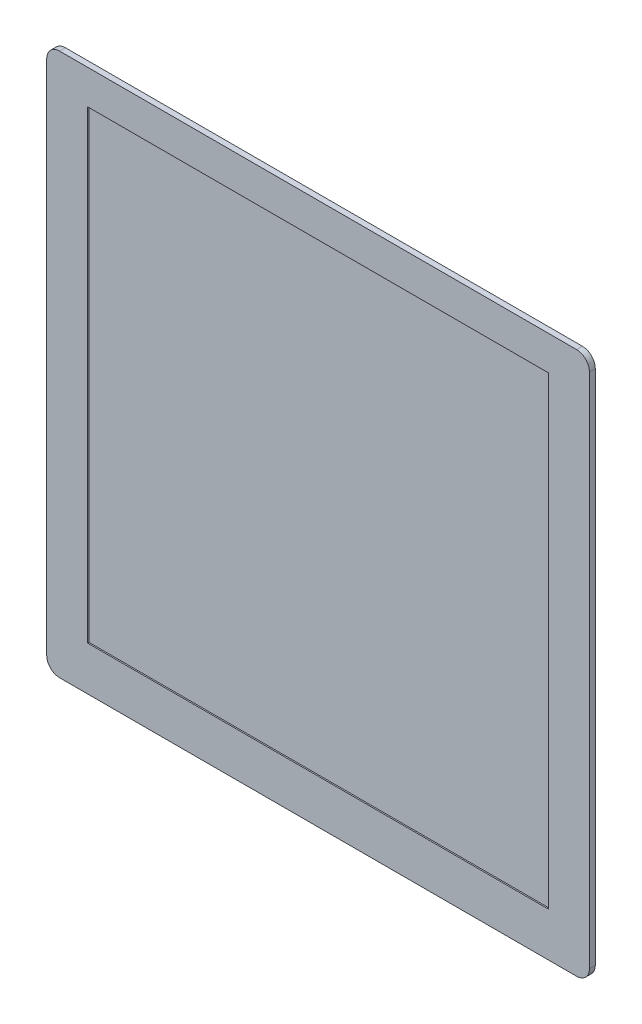
SolidWorks part; units mm, degrees
material "Plastique personnalisé"
ref_plane "Plan de face" through (0, 0, 0) normal (0, 0, 1) x (1, 0, 0)
ref_plane "Plan de dessus" through (0, 0, 0) normal (0, 1, 0) x (1, 0, 0)
ref_plane "Plan de droite" through (0, 0, 0) normal (1, 0, 0) x (0, 0, -1)
sketch "Esquisse1" plane through (0, 0, 0) normal (0, 0, 1) x (1, 0, 0)
  line L1 (2, 0) -> (82, 0)
  line L2 (0, 2) -> (0, 82)
  line L3 (2, 84) -> (82, 84)
  line L4 (84, 2) -> (84, 82)
  arc A0 (82, 0) -> (84, 2) centre (82, 2) ccw
  arc A1 (2, 0) -> (0, 2) centre (2, 2) cw
  arc A2 (0, 82) -> (2, 84) centre (2, 82) cw
  arc A3 (82, 84) -> (84, 82) centre (82, 82) cw
  point P7 (84, 0)
  point P10 (0, 0)
  point P13 (0, 84)
  point P16 (84, 84)
  dimension "D3" = 2
  dimension "D1" = 84
  dimension "D2" = 84
extrude "Boss.-Extru.1" add sketch "Esquisse1" against normal blind 0.9
sketch "Esquisse2" plane through (0, 0, -0.9) normal (0, 0, -1) x (-1, 0, 0)
  line L0 (-84.1401, 84) -> (-84.1401, 80.9998) construction
  line L1 (-84.1401, 80.9998) -> (0, 80.9998) construction
  line L2 (0, 82) -> (0, 2) construction
  line L3 (-84, 80.9998) -> (-80.0963, 80.9998) construction
  line L4 (-84, 2) -> (-84, 82) construction
  line L5 (-80.0963, 80.9998) -> (-80.0963, 0) construction
  line L6 (-2, 0) -> (-82, 0) construction
  line L7 (0, 80.9998) -> (-3.901, 80.9998) construction
  line L8 (-3.901, 80.9998) -> (-3.901, 0) construction
  line L9 (-3.901, 0) -> (-3.901, 1.3978) construction
  line L10 (-3.901, 1.3978) -> (-80.0963, 1.3978) construction
  line L12 (-80.0963, 80.9998) -> (-3.901, 80.9998)
  line L13 (-80.0963, 80.9998) -> (-80.0963, 1.3978)
  line L14 (-80.0963, 1.3978) -> (-3.901, 1.3978)
  line L15 (-3.901, 80.9998) -> (-3.901, 1.3978)
extrude "Boss.-Extru.2" add sketch "Esquisse2" along normal blind 1.7
sketch "Esquisse3" plane through (0, 0, 0) normal (0, 0, 1) x (1, 0, 0)
  line L0 (0, 84) -> (6.3086, 84) construction
  line L1 (82, 84) -> (2, 84) construction
  line L2 (6.3086, 84) -> (6.3086, 0) construction
  line L3 (2, 0) -> (82, 0) construction
  line L4 (84, 84) -> (77.6892, 84) construction
  line L5 (77.6892, 84) -> (77.6892, 0) construction
  line L6 (6.3086, 84) -> (6.3086, 78.7018) construction
  line L7 (6.3086, 78.7018) -> (77.6892, 78.7018) construction
  line L8 (6.3086, 0.0194) -> (6.3086, 6.819) construction
  line L9 (6.3086, 6.819) -> (77.6892, 6.819) construction
  line L11 (6.3086, 78.7018) -> (77.6892, 78.7018)
  line L12 (6.3086, 78.7018) -> (6.3086, 6.819)
  line L13 (6.3086, 6.819) -> (77.6892, 6.819)
  line L14 (77.6892, 78.7018) -> (77.6892, 6.819)
extrude "Enlèv. mat.-Extru.1" cut sketch "Esquisse3" against normal blind 0.2
sketch "Esquisse4" plane through (0, 0, -2.6) normal (0, 0, -1) x (-1, 0, 0)
  text T0 "720x720"
extrude "Enlèv. mat.-Extru.2" cut sketch "Esquisse4" against normal blind 0.1
sketch "Esquisse5" plane through (0, 0, -0.9) normal (0, 0, -1) x (-1, 0, 0)
  text T0 "T1238A - V2" font "@Arial Unicode MS" height in points 5
extrude "Enlèv. mat.-Extru.3" cut sketch "Esquisse5" against normal blind 0.1
